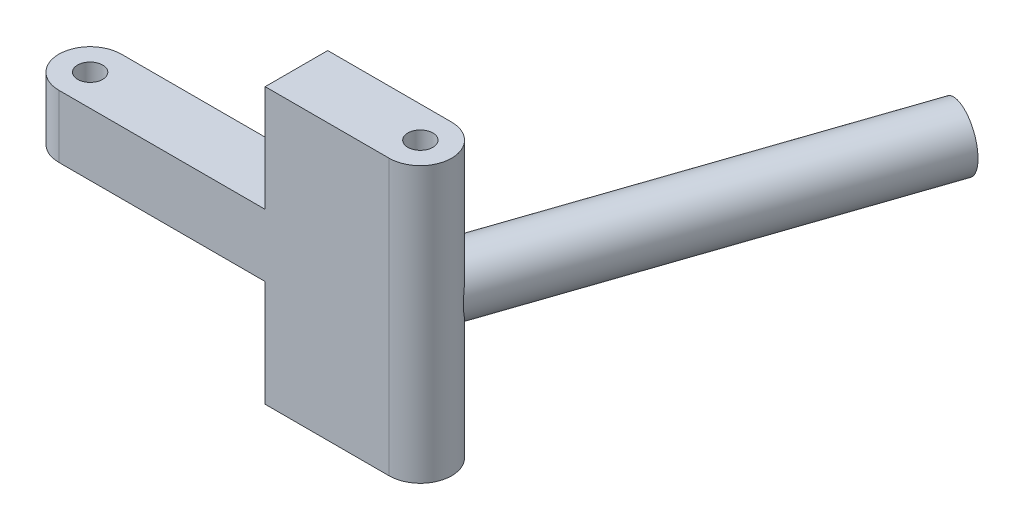
SolidWorks part; units mm, degrees
ref_plane "Front Plane" through (0, 0, 0) normal (0, 0, 1) x (1, 0, 0)
ref_plane "Top Plane" through (0, 0, 0) normal (0, 1, 0) x (1, 0, 0)
ref_plane "Right Plane" through (0, 0, 0) normal (1, 0, 0) x (0, 0, -1)
sketch "Sketch1" plane through (0, 0, 0) normal (0, 1, 0) x (1, 0, 0)
  line L0 (0, 0) -> (26.41, 0) construction
  line L1 (0, 2.5) -> (26.41, 2.5)
  line L2 (0, -2.5) -> (26.41, -2.5)
  arc A0 (0, 2.5) -> (0, -2.5) centre (0, 0) ccw
  arc A1 (26.41, -2.5) -> (26.41, 2.5) centre (26.41, 0) ccw
  point P3 (13.205, 0)
  dimension "D2" = 2.5
  dimension "D1" = 26.41
  dimension "D3" = 0
extrude "Boss-Extrude1" add sketch "Sketch1" along normal blind 22
sketch "Sketch2" plane through (0, 22, 0) normal (0, 1, 0) x (1, 0, 0)
  circle A0 centre (0, 0) radius 1
  circle A1 centre (26.41, 0) radius 1
  arc A2 (0, 2.5) -> (0, -2.5) centre (0, 0) ccw construction
  dimension "D1" = 0
  dimension "D2" = 2
  dimension "D3" = 2
extrude "Cut-Extrude1" cut sketch "Sketch2" against normal blind 22
ref_plane "Plane1" through (-2.5, 0, 0) normal (1, 0, 0) x (0, 0, -1)
sketch "Sketch3" plane through (-2.5, 0, 0) normal (1, 0, 0) x (0, 0, -1)
  line L0 (2.5, 22) -> (2.5, 0) construction
  line L1 (2.5, 13.5) -> (-2.5, 13.5)
  line L2 (2.5, 13.5) -> (2.5, 22)
  line L3 (2.5, 22) -> (-2.5, 22)
  line L4 (-2.5, 13.5) -> (-2.5, 22)
  line L6 (-2.5, 0) -> (2.5, 0)
  line L7 (-2.5, 0) -> (-2.5, 8.5)
  line L8 (-2.5, 8.5) -> (2.5, 8.5)
  line L9 (2.5, 0) -> (2.5, 8.5)
  dimension "D1" = 8.5
  dimension "D2" = 8.5
  dimension "D3" = 5
extrude "Cut-Extrude7" cut sketch "Sketch3" along normal blind 19
ref_plane "Plane3" through (3.496, 0, -10.2872) normal (0.3218, 0, -0.9468) x (0, -1, 0)
sketch "Sketch5" plane through (3.496, 0, -10.2872) normal (0.3218, 0, -0.9468) x (0, -1, 0)
  line L0 (-22, -24.201) -> (0, -24.201) construction
  circle A0 centre (-11, -24.201) radius 2.4
  dimension "D1" = 4.8
extrude "Boss-Extrude3" add sketch "Sketch5" along normal blind 32 and the other way up to next
